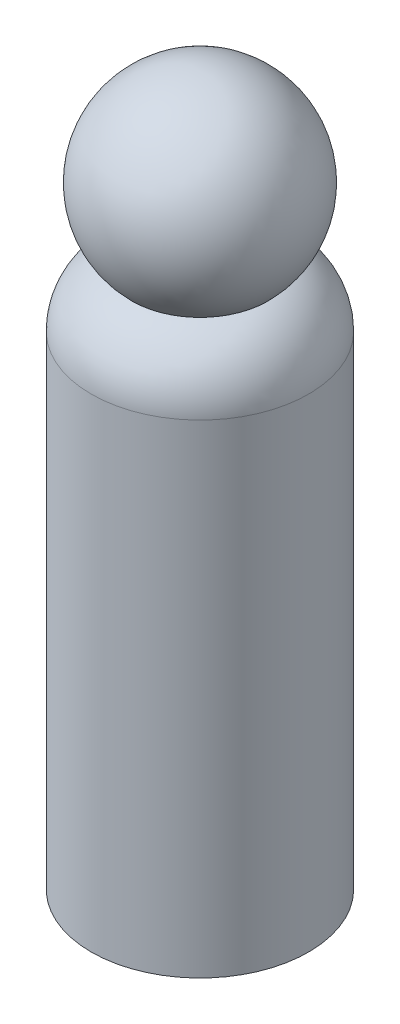
SolidWorks part; units mm, degrees
material "Beech"
ref_plane "Front Plane" through (0, 0, 0) normal (0, 0, 1) x (1, 0, 0)
ref_plane "Top Plane" through (0, 0, 0) normal (0, 1, 0) x (1, 0, 0)
ref_plane "Right Plane" through (0, 0, 0) normal (1, 0, 0) x (0, 0, -1)
sketch "Sketch1" plane through (0, 0, 0) normal (0, 0, 1) x (1, 0, 0)
  line L0 (0, 0) -> (-21.4312, 0)
  line L1 (-21.4312, 0) -> (-21.4312, 95.25)
  line L3 (0, 139.7) -> (0, 0)
  arc A0 (0, 139.7) -> (-13.3646, 107.0746) centre (0, 120.65) ccw
  arc A1 (-21.4312, 95.25) -> (-13.3646, 107.0746) centre (-8.7312, 95.25) cw
  point P9 (-21.4312, 107.95)
  dimension "D3" = 38.1
  dimension "D4" = 12.7
  dimension "D6" = 21.4312
  dimension "D7" = 95.25
  dimension "D1" = 107.95
  dimension "D2" = 21.4312
  dimension "D5" = 120.65
  dimension "D8" = 21.4312
revolve "Revolve1" add sketch "Sketch1" angle 360 about L3
